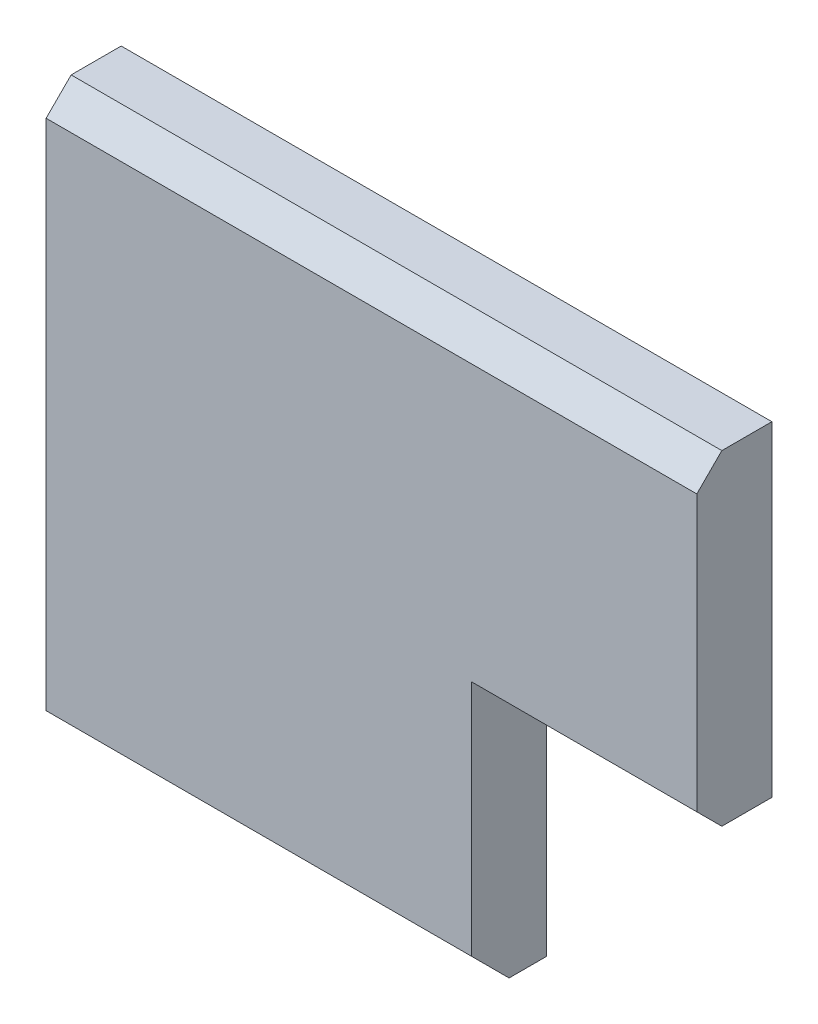
SolidWorks part; units mm, degrees
material "Стекло"
ref_plane "Front" through (0, 0, 0) normal (0, 0, 1) x (1, 0, 0)
ref_plane "Top" through (0, 0, 0) normal (0, 1, 0) x (1, 0, 0)
ref_plane "Right" through (0, 0, 0) normal (1, 0, 0) x (0, 0, -1)
sketch "Эскиз1" plane through (0, 0, 0) normal (0, 0, 1) x (1, 0, 0)
  line L0 (-13, 13) -> (13, 13)
  line L1 (13, 13) -> (13, -10)
  line L2 (13, -10) -> (-13, -10)
  line L3 (-13, -10) -> (-13, 13)
  dimension "D1" = 26
  dimension "D2" = 23
  dimension "D3" = 13
  dimension "D4" = 13
extrude "Вытянуть1" add sketch "Эскиз1" along normal blind 3
chamfer "Фаска1" distance 1.5 angle 45 1 edges at (0, -10, 3)
sketch "Эскиз2" plane through (0, 0, 0) normal (0, 0, -1) x (-1, 0, 0)
  line L0 (-13, 0) -> (-4, 0)
  line L1 (-13, -10) -> (-13, 13) construction
  line L2 (-4, 0) -> (-4, -10)
  line L3 (13, -10) -> (-13, -10) construction
  dimension "D1" = 10
  dimension "D2" = 9
extrude "Вырез-Вытянуть1" cut sketch "Эскиз2" against normal through all flip side to cut
chamfer "Фаска2" distance 1 angle 45 2 edges at (8.5, 0, 3) (0, 13, 3)
